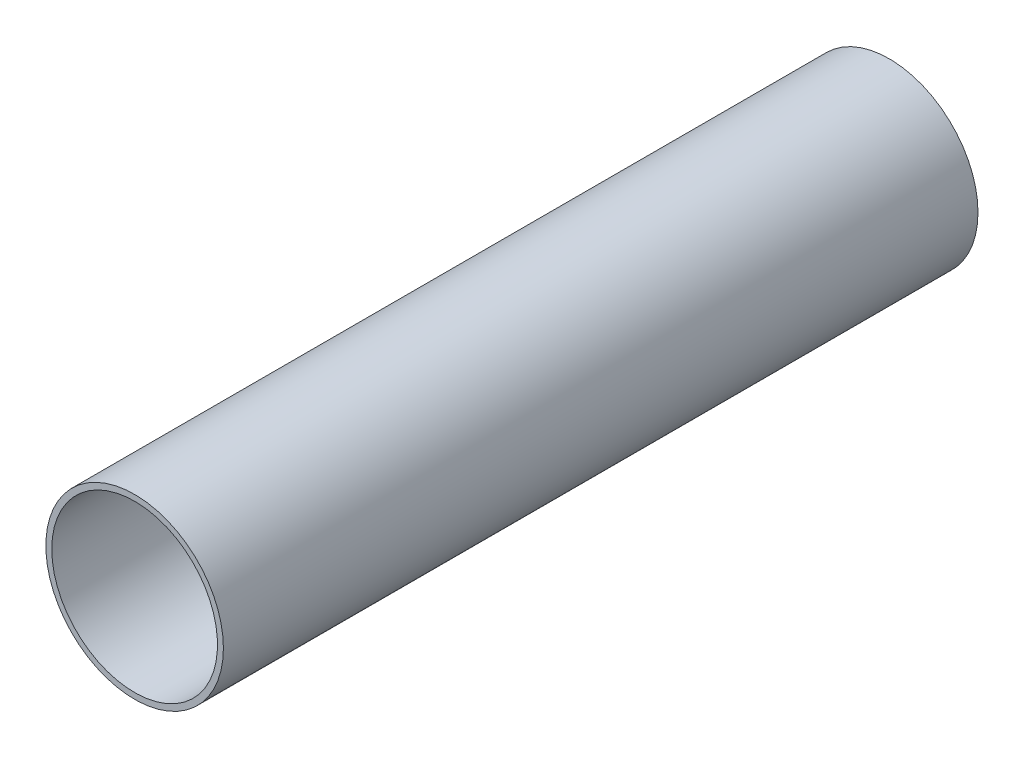
SolidWorks part; units mm, degrees
material "Plain Carbon Steel"
ref_plane "Front" through (0, 0, 0) normal (0, 0, 1) x (1, 0, 0)
ref_plane "Top" through (0, 0, 0) normal (0, 1, 0) x (1, 0, 0)
ref_plane "Right" through (0, 0, 0) normal (1, 0, 0) x (0, 0, -1)
sketch "Sketch1" plane through (0, 0, 0) normal (0, 0, 1) x (1, 0, 0)
  circle A0 centre (-13.8868, 18.2655) radius 50.8
  dimension "D1" = 101.6
extrude "Boss-Extrude1" add sketch "Sketch1" along normal blind 431.8
sketch "Sketch2" plane through (0, 0, 0) normal (0, 0, -1) x (-1, 0, 0)
  line L0 (64.6868, 18.2655) -> (-36.9132, 18.2655) construction
  circle A0 centre (13.8868, 18.2655) radius 50.8 construction
  circle A1 centre (13.8868, 18.2655) radius 47.4188
extrude "Cut-Extrude1" cut sketch "Sketch2" against normal blind 431.8
